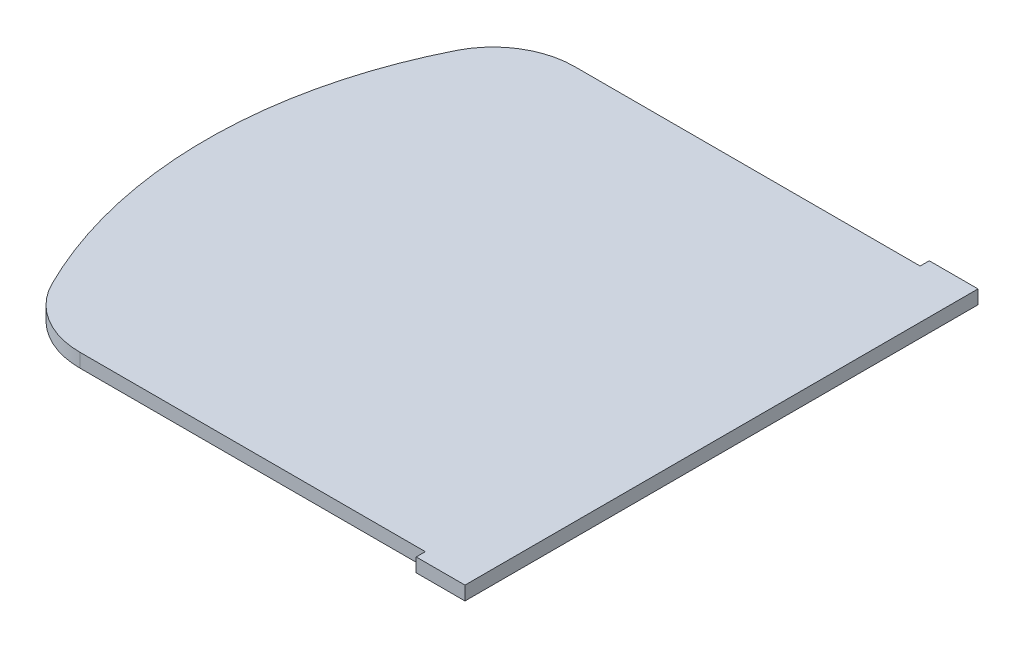
SolidWorks part; units mm, degrees
ref_plane "Front Plane" through (0, 0, 0) normal (0, 0, 1) x (1, 0, 0)
ref_plane "Top Plane" through (0, 0, 0) normal (0, 1, 0) x (1, 0, 0)
ref_plane "Right Plane" through (0, 0, 0) normal (1, 0, 0) x (0, 0, -1)
sketch "Sketch1" plane through (0, 0, 0) normal (0, 1, 0) x (1, 0, 0)
  line L0 (0, -242) -> (0, 242)
  line L1 (0, 242) -> (-46, 242)
  line L2 (-46, 242) -> (-46, 233.3873)
  line L3 (-46, 233.3873) -> (-372, 233.3873)
  line L4 (-486, 0) -> (0, 0) construction
  line L5 (-46, -233.3873) -> (-372, -233.3873)
  line L6 (-46, -242) -> (-46, -233.3873)
  line L7 (0, -242) -> (-46, -242)
  arc A0 (-372, 233.3873) -> (-440.8367, 190.8911) centre (-372, 156.3873) ccw
  arc A1 (-440.8367, 190.8911) -> (-440.8367, -190.8911) centre (-60, 0) ccw
  arc A2 (-372, -233.3873) -> (-440.8367, -190.8911) centre (-372, -156.3873) cw
  dimension "D4" = 77
  dimension "D6" = 426
  dimension "D5" = 60
  dimension "D1" = 242
  dimension "D2" = 46
  dimension "D3" = 372
extrude "Boss-Extrude1" add sketch "Sketch1" along normal mid plane 13
